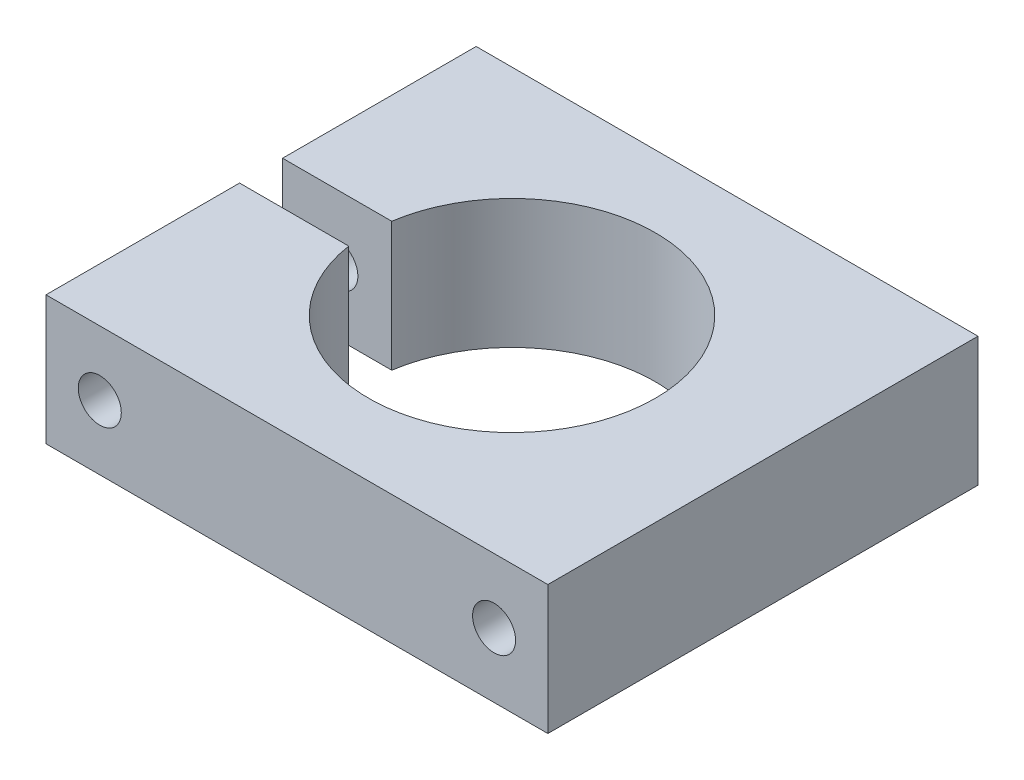
SolidWorks part; units mm, degrees
ref_plane "Front Plane" through (0, 0, 0) normal (0, 0, 1) x (1, 0, 0)
ref_plane "Top Plane" through (0, 0, 0) normal (0, 1, 0) x (1, 0, 0)
ref_plane "Right Plane" through (0, 0, 0) normal (1, 0, 0) x (0, 0, -1)
sketch "Sketch1" plane through (0, 0, 0) normal (0, 1, 0) x (1, 0, 0)
  line L0 (0, -267.977) -> (0, 13130.8724) construction
  line L1 (-35, 30) -> (35, 30)
  line L2 (-35, 30) -> (-35, 3)
  line L3 (-35, -30) -> (35, -30)
  line L4 (35, 30) -> (35, -30)
  line L5 (-35, 30) -> (35, -30) construction
  line L6 (-35, -30) -> (35, 30) construction
  line L7 (-267.977, 0) -> (13130.8724, 0) construction
  line L8 (-19.7737, 3) -> (-35, 3)
  line L9 (-19.7737, -3) -> (-35, -3)
  line L10 (-35, -3) -> (-35, -30)
  arc A0 (-19.7737, -3) -> (-19.7737, 3) centre (0, 0) ccw
  point P0 (0, 0)
  dimension "D3" = 40
  dimension "D1" = 60
  dimension "D2" = 70
  dimension "D4" = 3
extrude "Boss-Extrude1" add sketch "Sketch1" along normal blind 18
sketch "Sketch2" plane through (0, 0, 30) normal (0, 0, 1) x (1, 0, 0)
  line L0 (0, -1000) -> (0, 49000) construction
  line L1 (-1020, 9) -> (48980, 9) construction
  line L2 (-35, 18) -> (-35, 0) construction
  circle A0 centre (27.5, 9) radius 3
  circle A1 centre (-27.5, 9) radius 3
  point P8 (-35, 9)
  dimension "D1" = 6
  dimension "D2" = 27.5
extrude "Cut-Extrude1" cut sketch "Sketch2" against normal through all
